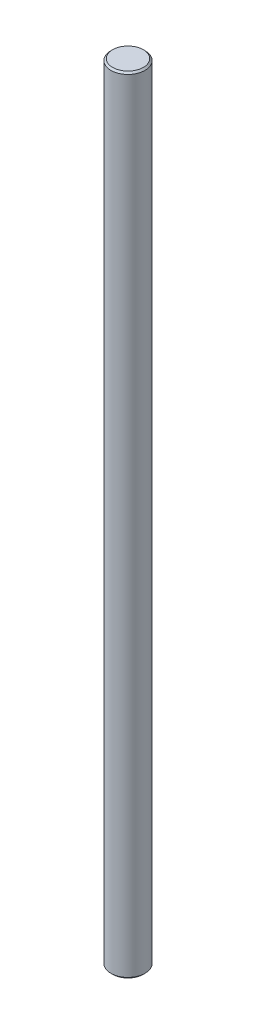
SolidWorks part; units mm, degrees
ref_plane "Front Plane" through (0, 0, 0) normal (0, 0, 1) x (1, 0, 0)
ref_plane "Top Plane" through (0, 0, 0) normal (0, 1, 0) x (1, 0, 0)
ref_plane "Right Plane" through (0, 0, 0) normal (1, 0, 0) x (0, 0, -1)
sketch "Sketch1" plane through (0, 0, 0) normal (0, 1, 0) x (1, 0, 0)
  circle A0 centre (0, 0) radius 5
  dimension "D1" = 10
extrude "Boss-Extrude1" add sketch "Sketch1" along normal blind 230
chamfer "Chamfer1" distance 0.5 angle 45 2 edges at (0, 0, 5) (0, 230, 5)
